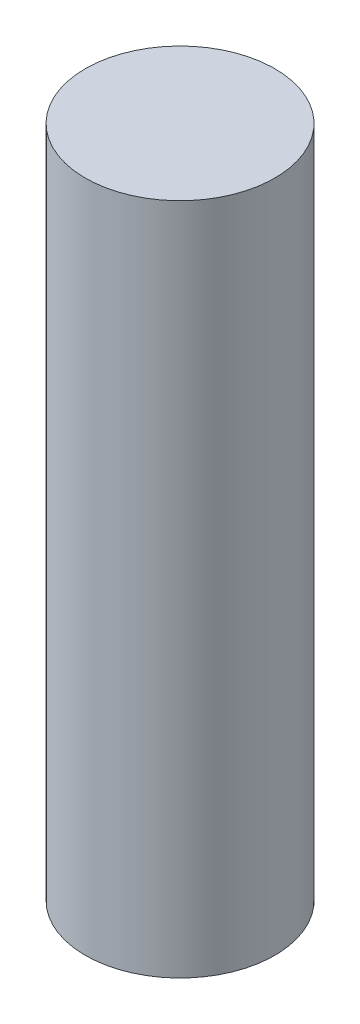
SolidWorks part; units mm, degrees
ref_plane "Front Plane" through (0, 0, 0) normal (0, 0, 1) x (1, 0, 0)
ref_plane "Top Plane" through (0, 0, 0) normal (0, 1, 0) x (1, 0, 0)
ref_plane "Right Plane" through (0, 0, 0) normal (1, 0, 0) x (0, 0, -1)
sketch "Sketch1" plane through (0, 0, 0) normal (0, 0, 1) x (1, 0, 0)
  line L0 (0, 32.5) -> (0, 49.7776) construction
  line L1 (-9.15, 32.5) -> (0, 32.5)
  line L2 (-9.15, 32.5) -> (-9.15, -32.5)
  line L3 (-9.15, -32.5) -> (0, -32.5)
  line L4 (0, 32.5) -> (0, -32.5)
  point P4 (0, 0)
  dimension "D1" = 65
  dimension "D2" = 18.3
revolve "Revolve1" add sketch "Sketch1" angle 360 about L4
